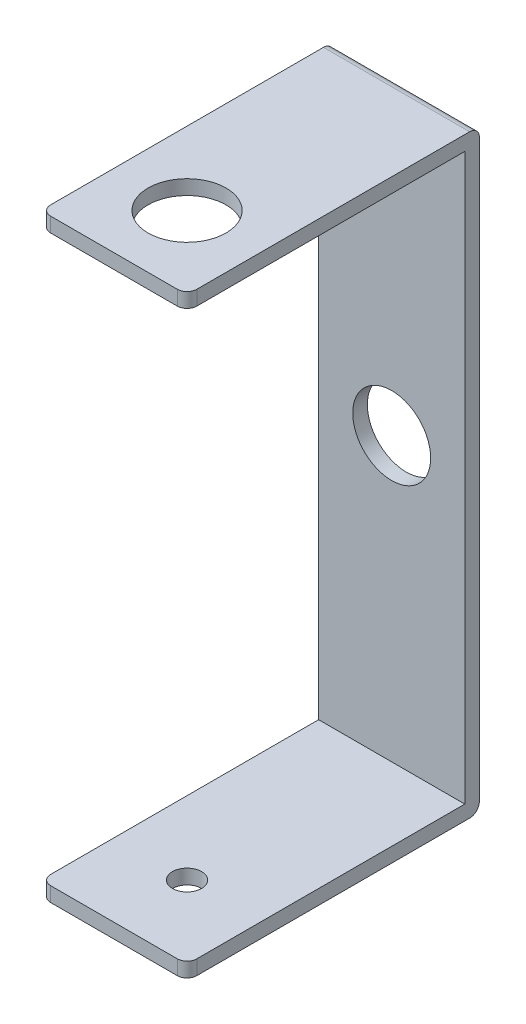
SolidWorks part; units mm, degrees
ref_plane "Front Plane" through (0, 0, 0) normal (0, 0, 1) x (1, 0, 0)
ref_plane "Top Plane" through (0, 0, 0) normal (0, 1, 0) x (1, 0, 0)
ref_plane "Right Plane" through (0, 0, 0) normal (1, 0, 0) x (0, 0, -1)
sketch "Sketch1" plane through (0, 0, 0) normal (0, 0, 1) x (1, 0, 0)
  line L1 (-7.5, -30.5) -> (7.5, -30.5)
  line L2 (-7.5, -30.5) -> (-7.5, 30.5)
  line L3 (-7.5, 30.5) -> (7.5, 30.5)
  line L4 (7.5, -30.5) -> (7.5, 30.5)
  line L5 (-7.5, -30.5) -> (7.5, 30.5) construction
  line L6 (-7.5, 30.5) -> (7.5, -30.5) construction
  line L7 (-7.5, 30.5) -> (7.5, 30.5)
  line L8 (-7.5, 30.5) -> (-7.5, 26.8473)
  line L10 (7.5, 30.5) -> (7.5, 26.8473)
  line L11 (7.5, -30.5) -> (-7.5, -30.5)
  line L12 (7.5, -30.5) -> (7.5, -23.0426)
  line L14 (-7.5, -30.5) -> (-7.5, -23.0426)
  circle A0 centre (0, 0) radius 4
  point P0 (0, 0)
  dimension "D3" = 8
  dimension "D1" = 15
  dimension "D2" = 61
extrude "Boss-Extrude1" add sketch "Sketch1" along normal blind 1.5
sketch "Sketch2" plane through (0, 0, 1.5) normal (0, 0, 1) x (1, 0, 0)
  line L0 (7.5, -30.5) -> (7.5, 30.5) construction
  line L1 (-7.5, 30.5) -> (7.5, 30.5)
  line L2 (-7.5, 30.5) -> (-7.5, 29)
  line L3 (-7.5, 29) -> (7.5, 29)
  line L4 (7.5, 30.5) -> (7.5, 29)
  line L5 (-7.5, -30.5) -> (-7.5, 30.5) construction
  line L6 (7.5, -30.5) -> (-7.5, -30.5)
  line L7 (7.5, -30.5) -> (7.5, -29)
  line L8 (7.5, -29) -> (-7.5, -29)
  line L9 (-7.5, -30.5) -> (-7.5, -29)
  dimension "D1" = 1.5
  dimension "D2" = 1.5
extrude "Boss-Extrude2" add sketch "Sketch2" along normal blind 28.5
sketch "Sketch3" plane through (0, 30.5, 0) normal (0, 1, 0) x (1, 0, 0)
  line L0 (7.5, -30) -> (-7.5, -30) construction
  circle A0 centre (0, -22.5) radius 1.5
  dimension "D2" = 3
  dimension "D1" = 7.5
extrude "Cut-Extrude1" cut sketch "Sketch3" against normal through all
fillet "Fillet1" radius 1 6 edges at (0, -30.5, 0) (-7.5, -29.75, 30) (7.5, -29.75, 30) (7.5, 29.75, 30) (-7.5, 29.75, 30) (0, 30.5, 0)
sketch "Sketch5" plane through (0, 30.5, 0) normal (0, 1, 0) x (1, 0, 0)
  circle A0 centre (0, -22.5) radius 4
  dimension "D1" = 8
extrude "Cut-Extrude2" cut sketch "Sketch5" against normal up to next
